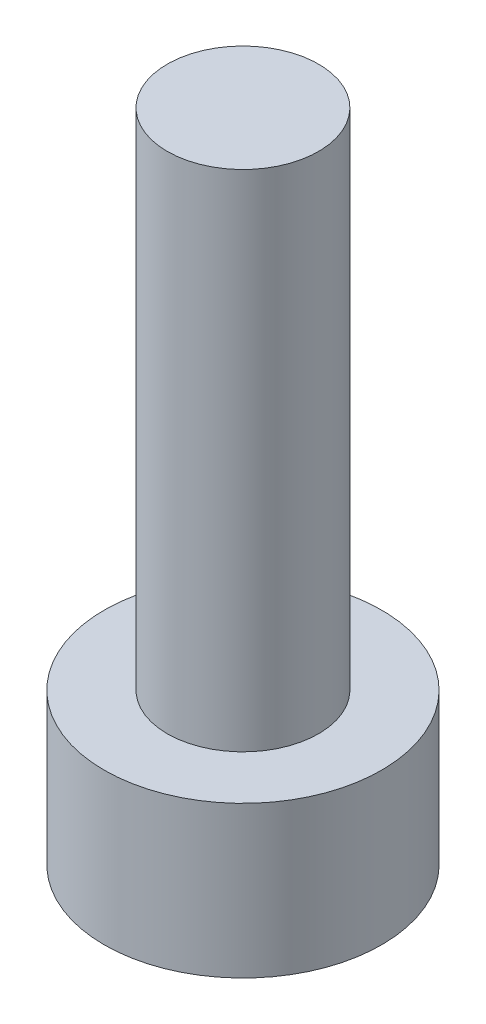
SolidWorks part; units mm, degrees
ref_plane "Front Plane" through (0, 0, 0) normal (0, 0, 1) x (1, 0, 0)
ref_plane "Top Plane" through (0, 0, 0) normal (0, 1, 0) x (1, 0, 0)
ref_plane "Right Plane" through (0, 0, 0) normal (1, 0, 0) x (0, 0, -1)
sketch "Sketch1" plane through (0, 0, 0) normal (0, 1, 0) x (1, 0, 0)
  circle A0 centre (0, 0) radius 2.75
  dimension "D1" = 5.5
extrude "Boss-Extrude1" add sketch "Sketch1" along normal blind 3
sketch "Sketch2" plane through (0, 3, 0) normal (0, 1, 0) x (1, 0, 0)
  circle A0 centre (0, 0) radius 1.5
  dimension "D1" = 3
extrude "Boss-Extrude2" add sketch "Sketch2" along normal blind 10
sketch "Sketch3" plane through (0, 0, 0) normal (0, -1, 0) x (-1, 0, 0)
  line L1 (0, -1.4434) -> (1.25, -0.7217)
  line L2 (1.25, -0.7217) -> (1.25, 0.7217)
  line L3 (1.25, 0.7217) -> (0, 1.4434)
  line L4 (0, 1.4434) -> (-1.25, 0.7217)
  line L5 (-1.25, 0.7217) -> (-1.25, -0.7217)
  line L6 (-1.25, -0.7217) -> (0, -1.4434)
  circle A0 centre (0, 0) radius 1.25 construction
  dimension "D1" = 2.5
extrude "Cut-Extrude1" cut sketch "Sketch3" against normal blind 1.5
